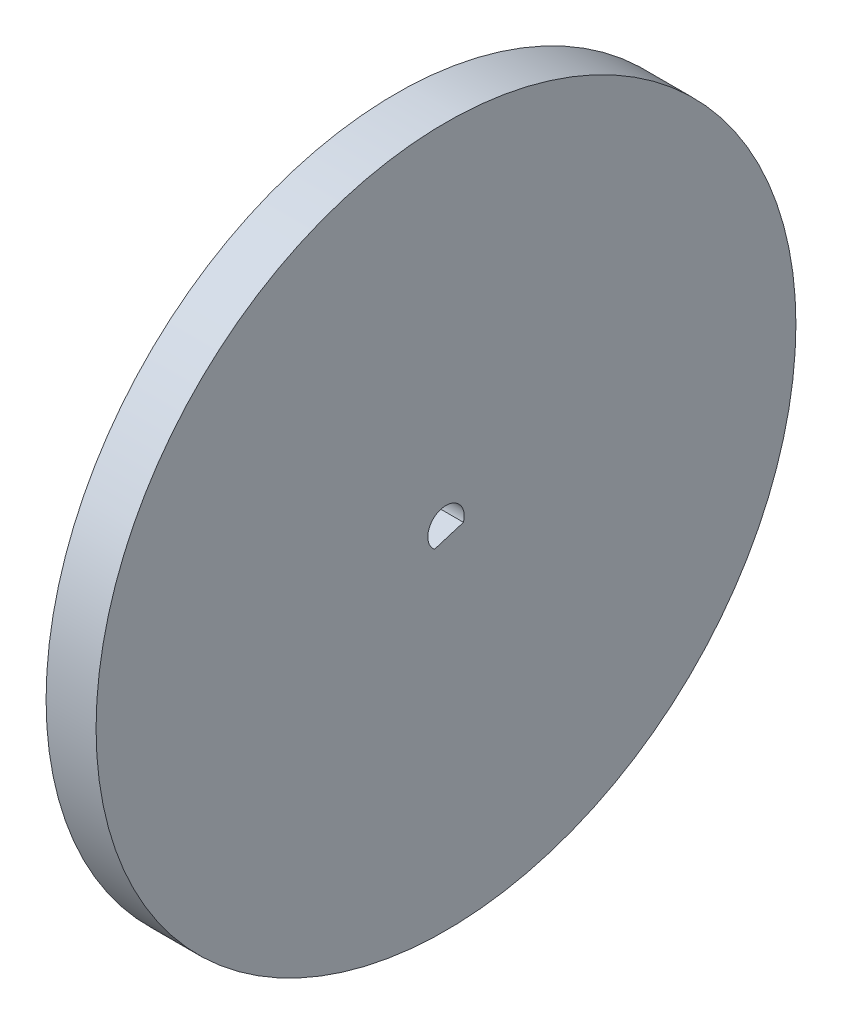
SolidWorks part; units mm, degrees
ref_plane "Front Plane" through (0, 0, 0) normal (0, 0, 1) x (1, 0, 0)
ref_plane "Top Plane" through (0, 0, 0) normal (0, 1, 0) x (1, 0, 0)
ref_plane "Right Plane" through (0, 0, 0) normal (1, 0, 0) x (0, 0, -1)
sketch "Sketch1" plane through (0, 0, 0) normal (1, 0, 0) x (0, 0, -1)
  circle A0 centre (0, 0) radius 44.45
  dimension "D1" = 88.9
extrude "Boss-Extrude1" add sketch "Sketch1" along normal blind 6.35
sketch "Sketch5" plane through (6.35, 0, 0) normal (1, 0, 0) x (0, 0, -1)
  line L1 (-1.4673, -1.7859) -> (2.2167, -0.6548)
  arc A3 (2.2167, -0.6548) -> (-1.4673, -1.7859) centre (0, 0) ccw
  dimension "D1" = 2.3114
  dimension "D2" = 3.6841
extrude "Cut-Extrude1" cut sketch "Sketch5" against normal through all
